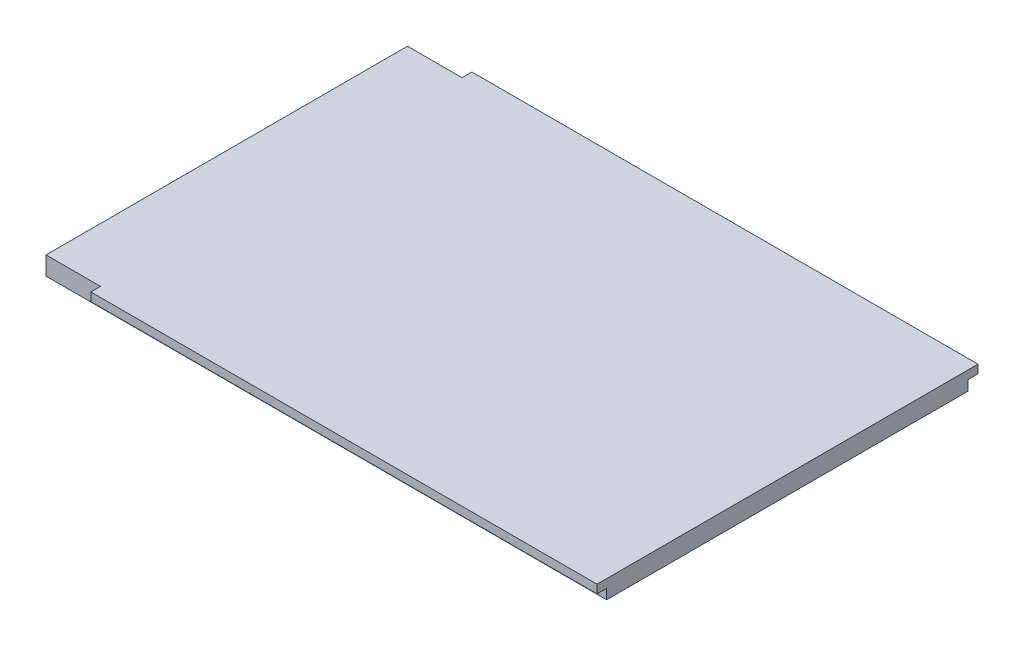
SolidWorks part; units mm, degrees
ref_plane "Plan de face" through (0, 0, 0) normal (0, 0, 1) x (1, 0, 0)
ref_plane "Plan de dessus" through (0, 0, 0) normal (0, 1, 0) x (1, 0, 0)
ref_plane "Plan de droite" through (0, 0, 0) normal (1, 0, 0) x (0, 0, -1)
sketch "Esquisse1" plane through (0, 0, 0) normal (0, 0, 1) x (1, 0, 0)
  line L0 (465.25, -20.1861) -> (-30.5, -20.1861) construction
  line L1 (0, -20.1861) -> (465.25, -20.1861)
  line L2 (0, -20.1861) -> (0, -4.9361)
  line L3 (0, -4.9361) -> (465.25, -4.9361)
  line L4 (465.25, -20.1861) -> (465.25, -4.9361)
  dimension "D1" = 15.25
extrude "Boss.-Extru.1" add sketch "Esquisse1" along normal up to surface (300 mm away)
sketch "Esquisse2" plane through (465.25, 0, 0) normal (1, 0, 0) x (0, 0, -1)
  line L0 (-300, -4.9361) -> (0, -4.9361) construction
  line L1 (-308, -4.9361) -> (8.1774, -4.9361)
  line L2 (-308, -4.9361) -> (-308, -11.9361)
  line L3 (-308, -11.9361) -> (8.1774, -11.9361)
  line L4 (8.1774, -4.9361) -> (8.1774, -11.9361)
  line L5 (-300, -20.1861) -> (-300, -4.9361) construction
  dimension "D1" = 7
  dimension "D2" = 8
extrude "Boss.-Extru.2" add sketch "Esquisse2" against normal blind 420
